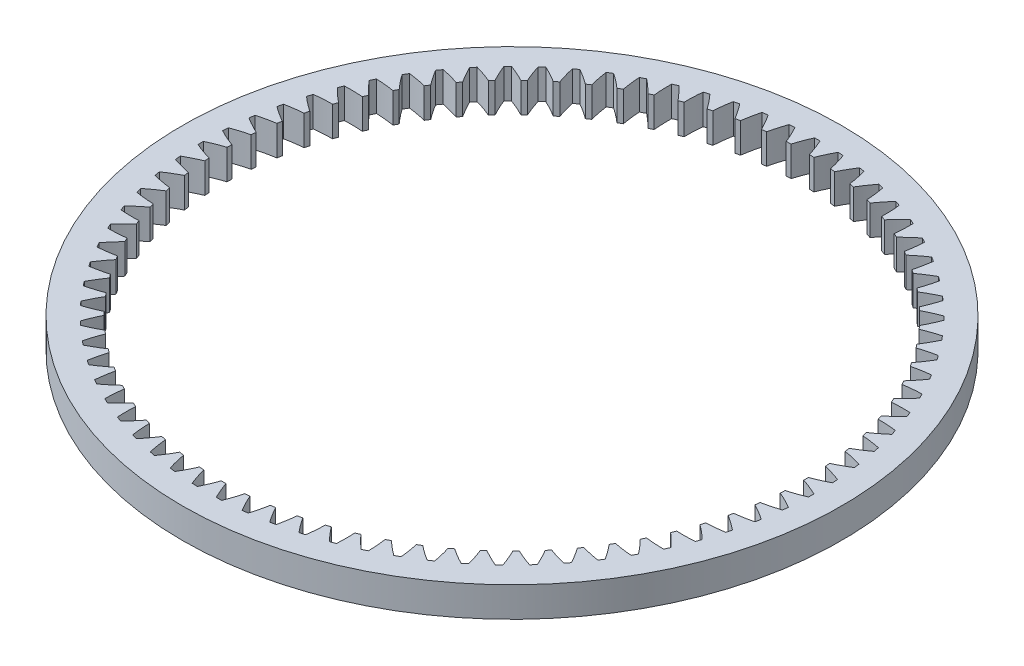
SolidWorks part; units mm, degrees
ref_plane "Front Plane" through (0, 0, 0) normal (0, 0, 1) x (1, 0, 0)
ref_plane "Top Plane" through (0, 0, 0) normal (0, 1, 0) x (1, 0, 0)
ref_plane "Right Plane" through (0, 0, 0) normal (1, 0, 0) x (0, 0, -1)
sketch "Sketch1" plane through (0, 0, 0) normal (0, 1, 0) x (1, 0, 0)
  line L0 (0, 52.5562) -> (0, -52.5562) construction
  circle A0 centre (0, 0) radius 29.5 construction
  circle A1 centre (0, 0) radius 30.56 construction
  arc A2 (-21.0185, 24.6048) -> (-21.4508, 24.2287) centre (0, 0) ccw
  circle A3 centre (0, 0) radius 34.925
  arc A4 (-0.2865, 32.3587) -> (-0.9677, 30.5447) centre (14.0429, 25.9432) ccw
  arc A5 (0.9677, 30.5447) -> (0.2865, 32.3587) centre (-14.0429, 25.9432) ccw
  arc A6 (-5.7937, 30.0058) -> (-6.2788, 29.908) centre (0, 0) ccw
  arc A7 (2.2853, 32.2792) -> (1.4622, 30.525) centre (16.0597, 24.7455) ccw
  arc A8 (3.3914, 30.3712) -> (2.8565, 32.2337) centre (-11.9373, 26.9769) ccw
  arc A9 (4.8427, 31.9956) -> (3.8828, 30.3123) centre (17.9749, 23.3913) ccw
  arc A10 (5.7937, 30.0058) -> (5.4084, 31.9048) centre (-9.7562, 27.84) ccw
  arc A11 (7.3694, 31.5097) -> (6.2788, 29.908) centre (19.7765, 21.8892) ccw
  arc A12 (8.1593, 29.4506) -> (7.9262, 31.3743) centre (-7.5135, 28.5271) ccw
  arc A13 (9.8496, 30.8246) -> (8.6352, 29.3146) centre (21.4531, 20.2488) ccw
  arc A14 (10.4734, 28.7093) -> (10.3938, 30.6454) centre (-5.2233, 29.0339) ccw
  arc A15 (12.2675, 29.9446) -> (10.9369, 28.5359) centre (22.9941, 18.4803) ccw
  arc A16 (12.7212, 27.7864) -> (12.7957, 29.7227) centre (-2.9, 29.3571) ccw
  arc A17 (14.6078, 28.8753) -> (13.1695, 27.5768) centre (24.3897, 16.595) ccw
  arc A18 (14.8887, 26.6879) -> (15.1168, 28.6121) centre (-0.5584, 29.4947) ccw
  arc A19 (16.8558, 27.6234) -> (15.3189, 26.4433) centre (25.631, 14.6048) ccw
  arc A20 (16.9619, 25.4206) -> (17.3422, 27.3206) centre (1.7867, 29.4458) ccw
  arc A21 (18.9972, 26.1969) -> (17.3714, 25.1426) centre (26.7104, 12.5222) ccw
  arc A22 (18.928, 23.9926) -> (19.458, 25.8564) centre (4.1206, 29.2108) ccw
  arc A23 (21.0185, 24.6048) -> (19.314, 23.6829) centre (27.6208, 10.3605) ccw
  arc A24 (20.7744, 22.4129) -> (21.4508, 24.2287) centre (6.4283, 28.7911) ccw
  arc A25 (22.9069, 22.8571) -> (21.1346, 22.0736) centre (28.3567, 8.1333) ccw
  arc A26 (22.4894, 20.6915) -> (23.308, 22.4479) centre (8.6955, 28.1893) ccw
  arc A27 (24.6504, 20.9649) -> (22.8215, 20.3247) centre (28.9132, 5.8546) ccw
  arc A28 (24.0623, 18.8393) -> (25.0178, 20.5251) centre (10.9076, 27.4094) ccw
  arc A29 (26.2382, 18.9401) -> (24.3642, 18.4472) centre (29.287, 3.539) ccw
  arc A30 (25.483, 16.868) -> (26.5694, 18.4725) centre (13.0508, 26.4561) ccw
  arc A31 (27.66, 16.7956) -> (25.7528, 16.4532) centre (29.4755, 1.2009) ccw
  arc A32 (26.7426, 14.7901) -> (27.9531, 16.3032) centre (15.1115, 25.3356) ccw
  arc A33 (28.907, 14.5449) -> (26.9786, 14.3551) centre (29.4778, -1.1447) ccw
  arc A34 (27.8331, 12.6186) -> (29.16, 14.0308) centre (17.0767, 24.0549) ccw
  arc A35 (29.9712, 12.2023) -> (28.0338, 12.1663) centre (29.2937, -3.4831) ccw
  arc A36 (28.7477, 10.3674) -> (30.1826, 11.6697) centre (18.9338, 22.6221) ccw
  arc A37 (30.846, 9.7825) -> (28.9118, 9.9005) centre (28.9243, -5.7995) ccw
  arc A38 (29.4805, 8.0506) -> (31.0143, 9.2348) centre (20.6713, 21.0463) ccw
  arc A39 (31.5257, 7.3008) -> (29.607, 7.5722) centre (28.3721, -8.0792) ccw
  arc A40 (30.027, 5.6829) -> (31.65, 6.7415) centre (22.2781, 19.3374) ccw
  arc A41 (32.0061, 4.773) -> (30.115, 5.1959) centre (27.6405, -10.3078) ccw
  arc A42 (30.3835, 3.2793) -> (32.0856, 4.2056) centre (23.744, 17.5063) ccw
  arc A43 (32.2841, 2.2151) -> (30.4327, 2.7869) centre (26.7342, -12.4713) ccw
  arc A44 (30.548, 0.855) -> (32.3183, 1.6431) centre (25.0599, 15.5645) ccw
  arc A45 (32.358, -0.3569) -> (30.5579, 0.3602) centre (25.6588, -14.5559) ccw
  arc A46 (30.5194, -1.5748) -> (32.3466, -0.9298) centre (26.2172, 13.5243) ccw
  arc A47 (32.2274, -2.9266) -> (30.4899, -2.0688) centre (24.4213, -16.5485) ccw
  arc A48 (30.2978, -3.9946) -> (32.1705, -3.4968) centre (27.2089, 11.3986) ccw
  arc A49 (31.893, -5.4779) -> (30.2291, -4.4847) centre (23.0293, -18.4364) ccw
  arc A50 (29.8847, -6.3891) -> (31.791, -6.0417) centre (28.0285, 9.2008) ccw
  arc A51 (31.357, -7.9944) -> (29.7773, -6.8722) centre (21.4917, -20.2078) ccw
  arc A52 (29.2826, -8.7433) -> (31.2105, -8.5484) centre (28.6709, 6.9448) ccw
  arc A53 (30.6227, -10.4605) -> (29.1372, -9.2163) centre (19.8182, -21.8515) ccw
  arc A54 (28.4954, -11.0421) -> (30.4326, -11.0011) centre (29.132, 4.645) ccw
  arc A55 (29.6948, -12.8604) -> (28.3128, -11.5021) centre (18.0195, -23.357) ccw
  arc A56 (27.528, -13.2712) -> (29.4624, -13.3842) centre (29.409, 2.3157) ccw
  arc A57 (28.5791, -15.179) -> (27.3095, -13.7152) centre (16.1068, -24.7148) ccw
  arc A58 (26.3866, -15.4163) -> (28.3059, -15.6827) centre (29.5, -0.0281) ccw
  arc A59 (27.2828, -17.4016) -> (26.1335, -15.8416) centre (14.0923, -25.9163) ccw
  arc A60 (25.0783, -17.464) -> (26.9704, -17.882) centre (29.4045, -2.3718) ccw
  arc A61 (25.814, -19.5143) -> (24.7922, -17.8678) centre (11.9887, -26.9541) ccw
  arc A62 (23.6115, -19.4013) -> (25.4644, -19.9683) centre (29.1231, -4.7005) ccw
  arc A63 (24.182, -21.5035) -> (23.2943, -19.7811) centre (9.8093, -27.8214) ccw
  arc A64 (21.9954, -21.2159) -> (23.7975, -21.9283) centre (28.6576, -6.9995) ccw
  arc A65 (22.3971, -23.3568) -> (21.649, -21.5693) centre (7.5679, -28.5128) ccw
  arc A66 (20.2403, -22.8964) -> (21.98, -23.7497) centre (28.0109, -9.2542) ccw
  arc A67 (20.4706, -25.0624) -> (19.8669, -23.2211) centre (5.2786, -29.0239) ccw
  arc A68 (18.3572, -24.4321) -> (20.0236, -25.4209) centre (27.1871, -11.4504) ccw
  arc A69 (18.4147, -26.6096) -> (17.9592, -24.7261) centre (2.956, -29.3515) ccw
  arc A70 (16.358, -25.8133) -> (17.9406, -26.9315) centre (26.1914, -13.5743) ccw
  arc A71 (16.2423, -27.9885) -> (15.9379, -26.0748) centre (0.6146, -29.4936) ccw
  arc A72 (14.2555, -27.0314) -> (15.7442, -28.2717) centre (25.0301, -15.6123) ccw
  arc A73 (13.9673, -29.1905) -> (13.8159, -27.2587) centre (-1.7306, -29.4492) ccw
  arc A74 (12.0628, -28.0785) -> (13.4483, -29.4332) centre (23.7106, -17.5515) ccw
  arc A75 (11.604, -30.2079) -> (11.6065, -28.2702) centre (-4.0648, -29.2186) ccw
  arc A76 (9.7938, -28.9482) -> (11.0673, -30.4086) centre (22.2412, -19.3799) ccw
  arc A77 (9.1673, -31.0344) -> (9.3237, -29.103) centre (-6.3734, -28.8033) ccw
  arc A78 (7.4629, -29.6348) -> (8.6163, -31.1918) centre (20.6311, -21.0857) ccw
  arc A79 (6.6726, -31.6646) -> (6.982, -29.7517) centre (-8.6417, -28.2059) ccw
  arc A80 (5.0848, -30.134) -> (6.1109, -31.7778) centre (18.8907, -22.6582) ccw
  arc A81 (4.1357, -32.0946) -> (4.5962, -30.2124) centre (-10.8553, -27.4301) ccw
  arc A82 (2.6746, -30.4427) -> (3.5668, -32.1628) centre (17.0308, -24.0874) ccw
  arc A83 (1.5727, -32.3218) -> (2.1813, -30.4821) centre (-13.0003, -26.481) ccw
  arc A84 (0.2474, -30.559) -> (1.0002, -32.3445) centre (15.0632, -25.3644) ccw
  arc A85 (-1.0002, -32.3445) -> (-0.2474, -30.559) centre (-15.0632, -25.3644) ccw
  arc A86 (-2.1813, -30.4821) -> (-1.5727, -32.3218) centre (13.0003, -26.481) ccw
  arc A87 (-3.5668, -32.1628) -> (-2.6746, -30.4427) centre (-17.0308, -24.0874) ccw
  arc A88 (-4.5962, -30.2124) -> (-4.1357, -32.0946) centre (10.8553, -27.4301) ccw
  arc A89 (-6.1109, -31.7778) -> (-5.0848, -30.134) centre (-18.8907, -22.6582) ccw
  arc A90 (-6.982, -29.7517) -> (-6.6726, -31.6646) centre (8.6417, -28.2059) ccw
  arc A91 (-8.6163, -31.1918) -> (-7.4629, -29.6348) centre (-20.6311, -21.0857) ccw
  arc A92 (-9.3237, -29.103) -> (-9.1673, -31.0344) centre (6.3734, -28.8033) ccw
  arc A93 (-11.0673, -30.4086) -> (-9.7938, -28.9482) centre (-22.2412, -19.3799) ccw
  arc A94 (-11.6065, -28.2702) -> (-11.604, -30.2079) centre (4.0648, -29.2186) ccw
  arc A95 (-13.4483, -29.4332) -> (-12.0628, -28.0785) centre (-23.7106, -17.5515) ccw
  arc A96 (-13.8159, -27.2587) -> (-13.9673, -29.1905) centre (1.7306, -29.4492) ccw
  arc A97 (-15.7442, -28.2717) -> (-14.2555, -27.0314) centre (-25.0301, -15.6123) ccw
  arc A98 (-15.9379, -26.0748) -> (-16.2423, -27.9885) centre (-0.6146, -29.4936) ccw
  arc A99 (-17.9406, -26.9315) -> (-16.358, -25.8133) centre (-26.1914, -13.5743) ccw
  arc A100 (-17.9592, -24.7261) -> (-18.4147, -26.6096) centre (-2.956, -29.3515) ccw
  arc A101 (-20.0236, -25.4209) -> (-18.3572, -24.4321) centre (-27.1871, -11.4504) ccw
  arc A102 (-19.8669, -23.2211) -> (-20.4706, -25.0624) centre (-5.2786, -29.0239) ccw
  arc A103 (-21.98, -23.7497) -> (-20.2403, -22.8964) centre (-28.0109, -9.2542) ccw
  arc A104 (-21.649, -21.5693) -> (-22.3971, -23.3568) centre (-7.5679, -28.5128) ccw
  arc A105 (-23.7975, -21.9283) -> (-21.9954, -21.2159) centre (-28.6576, -6.9995) ccw
  arc A106 (-23.2943, -19.7811) -> (-24.182, -21.5035) centre (-9.8093, -27.8214) ccw
  arc A107 (-25.4644, -19.9683) -> (-23.6115, -19.4013) centre (-29.1231, -4.7005) ccw
  arc A108 (-24.7922, -17.8678) -> (-25.814, -19.5143) centre (-11.9887, -26.9541) ccw
  arc A109 (-26.9704, -17.882) -> (-25.0783, -17.464) centre (-29.4045, -2.3718) ccw
  arc A110 (-26.1335, -15.8416) -> (-27.2828, -17.4016) centre (-14.0923, -25.9163) ccw
  arc A111 (-28.3059, -15.6827) -> (-26.3866, -15.4163) centre (-29.5, -0.0281) ccw
  arc A112 (-27.3095, -13.7152) -> (-28.5791, -15.179) centre (-16.1068, -24.7148) ccw
  arc A113 (-29.4624, -13.3842) -> (-27.528, -13.2712) centre (-29.409, 2.3157) ccw
  arc A114 (-28.3128, -11.5021) -> (-29.6948, -12.8604) centre (-18.0195, -23.357) ccw
  arc A115 (-30.4326, -11.0011) -> (-28.4954, -11.0421) centre (-29.132, 4.645) ccw
  arc A116 (-29.1372, -9.2163) -> (-30.6227, -10.4605) centre (-19.8182, -21.8515) ccw
  arc A117 (-31.2105, -8.5484) -> (-29.2826, -8.7433) centre (-28.6709, 6.9448) ccw
  arc A118 (-29.7773, -6.8722) -> (-31.357, -7.9944) centre (-21.4917, -20.2078) ccw
  arc A119 (-31.791, -6.0417) -> (-29.8847, -6.3891) centre (-28.0285, 9.2008) ccw
  arc A120 (-30.2291, -4.4847) -> (-31.893, -5.4779) centre (-23.0293, -18.4364) ccw
  arc A121 (-32.1705, -3.4968) -> (-30.2978, -3.9946) centre (-27.2089, 11.3986) ccw
  arc A122 (-30.4899, -2.0688) -> (-32.2274, -2.9266) centre (-24.4213, -16.5485) ccw
  arc A123 (-32.3466, -0.9298) -> (-30.5194, -1.5748) centre (-26.2172, 13.5243) ccw
  arc A124 (-30.5579, 0.3602) -> (-32.358, -0.3569) centre (-25.6588, -14.5559) ccw
  arc A125 (-32.3183, 1.6431) -> (-30.548, 0.855) centre (-25.0599, 15.5645) ccw
  arc A126 (-30.4327, 2.7869) -> (-32.2841, 2.2151) centre (-26.7342, -12.4713) ccw
  arc A127 (-32.0856, 4.2056) -> (-30.3835, 3.2793) centre (-23.744, 17.5063) ccw
  arc A128 (-30.115, 5.1959) -> (-32.0061, 4.773) centre (-27.6405, -10.3078) ccw
  arc A129 (-31.65, 6.7415) -> (-30.027, 5.6829) centre (-22.2781, 19.3374) ccw
  arc A130 (-29.607, 7.5722) -> (-31.5257, 7.3008) centre (-28.3721, -8.0792) ccw
  arc A131 (-31.0143, 9.2348) -> (-29.4805, 8.0506) centre (-20.6713, 21.0463) ccw
  arc A132 (-28.9118, 9.9005) -> (-30.846, 9.7825) centre (-28.9243, -5.7995) ccw
  arc A133 (-30.1826, 11.6697) -> (-28.7477, 10.3674) centre (-18.9338, 22.6221) ccw
  arc A134 (-28.0338, 12.1663) -> (-29.9712, 12.2023) centre (-29.2937, -3.4831) ccw
  arc A135 (-29.16, 14.0308) -> (-27.8331, 12.6186) centre (-17.0767, 24.0549) ccw
  arc A136 (-26.9786, 14.3551) -> (-28.907, 14.5449) centre (-29.4778, -1.1447) ccw
  arc A137 (-27.9531, 16.3032) -> (-26.7426, 14.7901) centre (-15.1115, 25.3356) ccw
  arc A138 (-25.7528, 16.4532) -> (-27.66, 16.7956) centre (-29.4755, 1.2009) ccw
  arc A139 (-26.5694, 18.4725) -> (-25.483, 16.868) centre (-13.0508, 26.4561) ccw
  arc A140 (-24.3642, 18.4472) -> (-26.2382, 18.9401) centre (-29.287, 3.539) ccw
  arc A141 (-25.0178, 20.5251) -> (-24.0623, 18.8393) centre (-10.9076, 27.4094) ccw
  arc A142 (-22.8215, 20.3247) -> (-24.6504, 20.9649) centre (-28.9132, 5.8546) ccw
  arc A143 (-23.308, 22.4479) -> (-22.4894, 20.6915) centre (-8.6955, 28.1893) ccw
  arc A144 (-21.1346, 22.0736) -> (-22.9069, 22.8571) centre (-28.3567, 8.1333) ccw
  arc A145 (-21.4508, 24.2287) -> (-20.7744, 22.4129) centre (-6.4283, 28.7911) ccw
  arc A146 (-19.314, 23.6829) -> (-21.0185, 24.6048) centre (-27.6208, 10.3605) ccw
  arc A147 (-19.458, 25.8564) -> (-18.928, 23.9926) centre (-4.1206, 29.2108) ccw
  arc A148 (-17.3714, 25.1426) -> (-18.9972, 26.1969) centre (-26.7104, 12.5222) ccw
  arc A149 (-17.3422, 27.3206) -> (-16.9619, 25.4206) centre (-1.7867, 29.4458) ccw
  arc A150 (-15.3189, 26.4433) -> (-16.8558, 27.6234) centre (-25.631, 14.6048) ccw
  arc A151 (-15.1168, 28.6121) -> (-14.8887, 26.6879) centre (0.5584, 29.4947) ccw
  arc A152 (-13.1695, 27.5768) -> (-14.6078, 28.8753) centre (-24.3897, 16.595) ccw
  arc A153 (-12.7957, 29.7227) -> (-12.7212, 27.7864) centre (2.9, 29.3571) ccw
  arc A154 (-10.9369, 28.5359) -> (-12.2675, 29.9446) centre (-22.9941, 18.4803) ccw
  arc A155 (-10.3938, 30.6454) -> (-10.4734, 28.7093) centre (5.2233, 29.0339) ccw
  arc A156 (-8.6352, 29.3146) -> (-9.8496, 30.8246) centre (-21.4531, 20.2488) ccw
  arc A157 (-7.9262, 31.3743) -> (-8.1593, 29.4506) centre (7.5135, 28.5271) ccw
  arc A158 (-6.2788, 29.908) -> (-7.3694, 31.5097) centre (-19.7765, 21.8892) ccw
  arc A159 (-5.4084, 31.9048) -> (-5.7937, 30.0058) centre (9.7562, 27.84) ccw
  arc A160 (-3.8828, 30.3123) -> (-4.8427, 31.9956) centre (-17.9749, 23.3913) ccw
  arc A161 (-2.8565, 32.2337) -> (-3.3914, 30.3712) centre (11.9373, 26.9769) ccw
  arc A162 (-1.4622, 30.525) -> (-2.2853, 32.2792) centre (-16.0597, 24.7455) ccw
  arc A163 (-3.3914, 30.3712) -> (-3.8828, 30.3123) centre (0, 0) ccw
  arc A164 (-0.9677, 30.5447) -> (-1.4622, 30.525) centre (0, 0) ccw
  arc A165 (1.4622, 30.525) -> (0.9677, 30.5447) centre (0, 0) ccw
  arc A166 (3.8828, 30.3123) -> (3.3914, 30.3712) centre (0, 0) ccw
  arc A167 (6.2788, 29.908) -> (5.7937, 30.0058) centre (0, 0) ccw
  arc A168 (8.6352, 29.3146) -> (8.1593, 29.4506) centre (0, 0) ccw
  arc A169 (10.9369, 28.5359) -> (10.4734, 28.7093) centre (0, 0) ccw
  arc A170 (13.1695, 27.5768) -> (12.7212, 27.7864) centre (0, 0) ccw
  arc A171 (-8.1593, 29.4506) -> (-8.6352, 29.3146) centre (0, 0) ccw
  arc A172 (-10.4734, 28.7093) -> (-10.9369, 28.5359) centre (0, 0) ccw
  arc A173 (-12.7212, 27.7864) -> (-13.1695, 27.5768) centre (0, 0) ccw
  arc A174 (-14.8887, 26.6879) -> (-15.3189, 26.4433) centre (0, 0) ccw
  arc A175 (-16.9619, 25.4206) -> (-17.3714, 25.1426) centre (0, 0) ccw
  arc A176 (-18.928, 23.9926) -> (-19.314, 23.6829) centre (0, 0) ccw
  arc A177 (-20.7744, 22.4129) -> (-21.1346, 22.0736) centre (0, 0) ccw
  arc A178 (-18.9972, 26.1969) -> (-19.458, 25.8564) centre (0, 0) ccw
  arc A179 (-16.8558, 27.6234) -> (-17.3422, 27.3206) centre (0, 0) ccw
  arc A180 (-14.6078, 28.8753) -> (-15.1168, 28.6121) centre (0, 0) ccw
  arc A181 (-12.2675, 29.9446) -> (-12.7957, 29.7227) centre (0, 0) ccw
  arc A182 (-9.8496, 30.8246) -> (-10.3938, 30.6454) centre (0, 0) ccw
  arc A183 (-7.3694, 31.5097) -> (-7.9262, 31.3743) centre (0, 0) ccw
  arc A184 (-4.8427, 31.9956) -> (-5.4084, 31.9048) centre (0, 0) ccw
  arc A185 (-2.2853, 32.2792) -> (-2.8565, 32.2337) centre (0, 0) ccw
  arc A186 (0.2865, 32.3587) -> (-0.2865, 32.3587) centre (0, 0) ccw
  arc A187 (2.8565, 32.2337) -> (2.2853, 32.2792) centre (0, 0) ccw
  arc A188 (5.4084, 31.9048) -> (4.8427, 31.9956) centre (0, 0) ccw
  arc A189 (7.9262, 31.3743) -> (7.3694, 31.5097) centre (0, 0) ccw
  arc A190 (10.3938, 30.6454) -> (9.8496, 30.8246) centre (0, 0) ccw
  arc A191 (12.7957, 29.7227) -> (12.2675, 29.9446) centre (0, 0) ccw
  arc A192 (-22.9069, 22.8571) -> (-23.308, 22.4479) centre (0, 0) ccw
  arc A193 (-24.6504, 20.9649) -> (-25.0178, 20.5251) centre (0, 0) ccw
  arc A194 (-26.2382, 18.9401) -> (-26.5694, 18.4725) centre (0, 0) ccw
  arc A195 (-27.66, 16.7956) -> (-27.9531, 16.3032) centre (0, 0) ccw
  arc A196 (-28.907, 14.5449) -> (-29.16, 14.0308) centre (0, 0) ccw
  arc A197 (-29.9712, 12.2023) -> (-30.1826, 11.6697) centre (0, 0) ccw
  arc A198 (-30.846, 9.7825) -> (-31.0143, 9.2348) centre (0, 0) ccw
  arc A199 (-31.5257, 7.3008) -> (-31.65, 6.7415) centre (0, 0) ccw
  arc A200 (-32.0061, 4.773) -> (-32.0856, 4.2056) centre (0, 0) ccw
  arc A201 (-32.2841, 2.2151) -> (-32.3183, 1.6431) centre (0, 0) ccw
  arc A202 (-32.358, -0.3569) -> (-32.3466, -0.9298) centre (0, 0) ccw
  arc A203 (-32.2274, -2.9266) -> (-32.1705, -3.4968) centre (0, 0) ccw
  arc A204 (-31.893, -5.4779) -> (-31.791, -6.0417) centre (0, 0) ccw
  arc A205 (-31.357, -7.9944) -> (-31.2105, -8.5484) centre (0, 0) ccw
  arc A206 (-30.6227, -10.4605) -> (-30.4326, -11.0011) centre (0, 0) ccw
  arc A207 (-29.6948, -12.8604) -> (-29.4624, -13.3842) centre (0, 0) ccw
  arc A208 (-28.5791, -15.179) -> (-28.3059, -15.6827) centre (0, 0) ccw
  arc A209 (-27.528, -13.2712) -> (-27.3095, -13.7152) centre (0, 0) ccw
  arc A210 (-26.3866, -15.4163) -> (-26.1335, -15.8416) centre (0, 0) ccw
  arc A211 (-28.4954, -11.0421) -> (-28.3128, -11.5021) centre (0, 0) ccw
  arc A212 (-29.2826, -8.7433) -> (-29.1372, -9.2163) centre (0, 0) ccw
  arc A213 (-29.8847, -6.3891) -> (-29.7773, -6.8722) centre (0, 0) ccw
  arc A214 (-30.2978, -3.9946) -> (-30.2291, -4.4847) centre (0, 0) ccw
  arc A215 (-30.5194, -1.5748) -> (-30.4899, -2.0688) centre (0, 0) ccw
  arc A216 (-30.548, 0.855) -> (-30.5579, 0.3602) centre (0, 0) ccw
  arc A217 (-30.3835, 3.2793) -> (-30.4327, 2.7869) centre (0, 0) ccw
  arc A218 (-30.027, 5.6829) -> (-30.115, 5.1959) centre (0, 0) ccw
  arc A219 (-29.4805, 8.0506) -> (-29.607, 7.5722) centre (0, 0) ccw
  arc A220 (-28.7477, 10.3674) -> (-28.9118, 9.9005) centre (0, 0) ccw
  arc A221 (-27.8331, 12.6186) -> (-28.0338, 12.1663) centre (0, 0) ccw
  arc A222 (-26.7426, 14.7901) -> (-26.9786, 14.3551) centre (0, 0) ccw
  arc A223 (-25.483, 16.868) -> (-25.7528, 16.4532) centre (0, 0) ccw
  arc A224 (-24.0623, 18.8393) -> (-24.3642, 18.4472) centre (0, 0) ccw
  arc A225 (-22.4894, 20.6915) -> (-22.8215, 20.3247) centre (0, 0) ccw
  arc A226 (15.1168, 28.6121) -> (14.6078, 28.8753) centre (0, 0) ccw
  arc A227 (17.3422, 27.3206) -> (16.8558, 27.6234) centre (0, 0) ccw
  arc A228 (19.458, 25.8564) -> (18.9972, 26.1969) centre (0, 0) ccw
  arc A229 (21.4508, 24.2287) -> (21.0185, 24.6048) centre (0, 0) ccw
  arc A230 (23.308, 22.4479) -> (22.9069, 22.8571) centre (0, 0) ccw
  arc A231 (25.0178, 20.5251) -> (24.6504, 20.9649) centre (0, 0) ccw
  arc A232 (26.5694, 18.4725) -> (26.2382, 18.9401) centre (0, 0) ccw
  arc A233 (27.9531, 16.3032) -> (27.66, 16.7956) centre (0, 0) ccw
  arc A234 (29.16, 14.0308) -> (28.907, 14.5449) centre (0, 0) ccw
  arc A235 (30.1826, 11.6697) -> (29.9712, 12.2023) centre (0, 0) ccw
  arc A236 (31.0143, 9.2348) -> (30.846, 9.7825) centre (0, 0) ccw
  arc A237 (31.65, 6.7415) -> (31.5257, 7.3008) centre (0, 0) ccw
  arc A238 (32.0856, 4.2056) -> (32.0061, 4.773) centre (0, 0) ccw
  arc A239 (32.3183, 1.6431) -> (32.2841, 2.2151) centre (0, 0) ccw
  arc A240 (32.3466, -0.9298) -> (32.358, -0.3569) centre (0, 0) ccw
  arc A241 (32.1705, -3.4968) -> (32.2274, -2.9266) centre (0, 0) ccw
  arc A242 (31.791, -6.0417) -> (31.893, -5.4779) centre (0, 0) ccw
  arc A243 (31.2105, -8.5484) -> (31.357, -7.9944) centre (0, 0) ccw
  arc A244 (30.4326, -11.0011) -> (30.6227, -10.4605) centre (0, 0) ccw
  arc A245 (29.4624, -13.3842) -> (29.6948, -12.8604) centre (0, 0) ccw
  arc A246 (28.3059, -15.6827) -> (28.5791, -15.179) centre (0, 0) ccw
  arc A247 (26.1335, -15.8416) -> (26.3866, -15.4163) centre (0, 0) ccw
  arc A248 (27.3095, -13.7152) -> (27.528, -13.2712) centre (0, 0) ccw
  arc A249 (28.3128, -11.5021) -> (28.4954, -11.0421) centre (0, 0) ccw
  arc A250 (29.1372, -9.2163) -> (29.2826, -8.7433) centre (0, 0) ccw
  arc A251 (29.7773, -6.8722) -> (29.8847, -6.3891) centre (0, 0) ccw
  arc A252 (30.2291, -4.4847) -> (30.2978, -3.9946) centre (0, 0) ccw
  arc A253 (30.4899, -2.0688) -> (30.5194, -1.5748) centre (0, 0) ccw
  arc A254 (30.5579, 0.3602) -> (30.548, 0.855) centre (0, 0) ccw
  arc A255 (30.4327, 2.7869) -> (30.3835, 3.2793) centre (0, 0) ccw
  arc A256 (30.115, 5.1959) -> (30.027, 5.6829) centre (0, 0) ccw
  arc A257 (29.607, 7.5722) -> (29.4805, 8.0506) centre (0, 0) ccw
  arc A258 (28.9118, 9.9005) -> (28.7477, 10.3674) centre (0, 0) ccw
  arc A259 (28.0338, 12.1663) -> (27.8331, 12.6186) centre (0, 0) ccw
  arc A260 (26.9786, 14.3551) -> (26.7426, 14.7901) centre (0, 0) ccw
  arc A261 (25.7528, 16.4532) -> (25.483, 16.868) centre (0, 0) ccw
  arc A262 (24.3642, 18.4472) -> (24.0623, 18.8393) centre (0, 0) ccw
  arc A263 (22.8215, 20.3247) -> (22.4894, 20.6915) centre (0, 0) ccw
  arc A264 (21.1346, 22.0736) -> (20.7744, 22.4129) centre (0, 0) ccw
  arc A265 (19.314, 23.6829) -> (18.928, 23.9926) centre (0, 0) ccw
  arc A266 (17.3714, 25.1426) -> (16.9619, 25.4206) centre (0, 0) ccw
  arc A267 (15.3189, 26.4433) -> (14.8887, 26.6879) centre (0, 0) ccw
  arc A268 (-27.2828, -17.4016) -> (-26.9704, -17.882) centre (0, 0) ccw
  arc A269 (-25.814, -19.5143) -> (-25.4644, -19.9683) centre (0, 0) ccw
  arc A270 (-24.182, -21.5035) -> (-23.7975, -21.9283) centre (0, 0) ccw
  arc A271 (-22.3971, -23.3568) -> (-21.98, -23.7497) centre (0, 0) ccw
  arc A272 (-20.4706, -25.0624) -> (-20.0236, -25.4209) centre (0, 0) ccw
  arc A273 (-18.4147, -26.6096) -> (-17.9406, -26.9315) centre (0, 0) ccw
  arc A274 (-16.2423, -27.9885) -> (-15.7442, -28.2717) centre (0, 0) ccw
  arc A275 (-13.9673, -29.1905) -> (-13.4483, -29.4332) centre (0, 0) ccw
  arc A276 (-11.604, -30.2079) -> (-11.0673, -30.4086) centre (0, 0) ccw
  arc A277 (-9.1673, -31.0344) -> (-8.6163, -31.1918) centre (0, 0) ccw
  arc A278 (-6.6726, -31.6646) -> (-6.1109, -31.7778) centre (0, 0) ccw
  arc A279 (-4.1357, -32.0946) -> (-3.5668, -32.1628) centre (0, 0) ccw
  arc A280 (-1.5727, -32.3218) -> (-1.0002, -32.3445) centre (0, 0) ccw
  arc A281 (1.0002, -32.3445) -> (1.5727, -32.3218) centre (0, 0) ccw
  arc A282 (3.5668, -32.1628) -> (4.1357, -32.0946) centre (0, 0) ccw
  arc A283 (6.1109, -31.7778) -> (6.6726, -31.6646) centre (0, 0) ccw
  arc A284 (8.6163, -31.1918) -> (9.1673, -31.0344) centre (0, 0) ccw
  arc A285 (11.0673, -30.4086) -> (11.604, -30.2079) centre (0, 0) ccw
  arc A286 (13.4483, -29.4332) -> (13.9673, -29.1905) centre (0, 0) ccw
  arc A287 (15.7442, -28.2717) -> (16.2423, -27.9885) centre (0, 0) ccw
  arc A288 (17.9406, -26.9315) -> (18.4147, -26.6096) centre (0, 0) ccw
  arc A289 (20.0236, -25.4209) -> (20.4706, -25.0624) centre (0, 0) ccw
  arc A290 (21.98, -23.7497) -> (22.3971, -23.3568) centre (0, 0) ccw
  arc A291 (23.7975, -21.9283) -> (24.182, -21.5035) centre (0, 0) ccw
  arc A292 (25.4644, -19.9683) -> (25.814, -19.5143) centre (0, 0) ccw
  arc A293 (26.9704, -17.882) -> (27.2828, -17.4016) centre (0, 0) ccw
  arc A294 (24.7922, -17.8678) -> (25.0783, -17.464) centre (0, 0) ccw
  arc A295 (23.2943, -19.7811) -> (23.6115, -19.4013) centre (0, 0) ccw
  arc A296 (21.649, -21.5693) -> (21.9954, -21.2159) centre (0, 0) ccw
  arc A297 (19.8669, -23.2211) -> (20.2403, -22.8964) centre (0, 0) ccw
  arc A298 (17.9592, -24.7261) -> (18.3572, -24.4321) centre (0, 0) ccw
  arc A299 (15.9379, -26.0748) -> (16.358, -25.8133) centre (0, 0) ccw
  arc A300 (13.8159, -27.2587) -> (14.2555, -27.0314) centre (0, 0) ccw
  arc A301 (11.6065, -28.2702) -> (12.0628, -28.0785) centre (0, 0) ccw
  arc A302 (9.3237, -29.103) -> (9.7938, -28.9482) centre (0, 0) ccw
  arc A303 (6.982, -29.7517) -> (7.4629, -29.6348) centre (0, 0) ccw
  arc A304 (4.5962, -30.2124) -> (5.0848, -30.134) centre (0, 0) ccw
  arc A305 (2.1813, -30.4821) -> (2.6746, -30.4427) centre (0, 0) ccw
  arc A306 (-0.2474, -30.559) -> (0.2474, -30.559) centre (0, 0) ccw
  arc A307 (-2.6746, -30.4427) -> (-2.1813, -30.4821) centre (0, 0) ccw
  arc A308 (-5.0848, -30.134) -> (-4.5962, -30.2124) centre (0, 0) ccw
  arc A309 (-7.4629, -29.6348) -> (-6.982, -29.7517) centre (0, 0) ccw
  arc A310 (-9.7938, -28.9482) -> (-9.3237, -29.103) centre (0, 0) ccw
  arc A311 (-12.0628, -28.0785) -> (-11.6065, -28.2702) centre (0, 0) ccw
  arc A312 (-14.2555, -27.0314) -> (-13.8159, -27.2587) centre (0, 0) ccw
  arc A313 (-16.358, -25.8133) -> (-15.9379, -26.0748) centre (0, 0) ccw
  arc A314 (-18.3572, -24.4321) -> (-17.9592, -24.7261) centre (0, 0) ccw
  arc A315 (-20.2403, -22.8964) -> (-19.8669, -23.2211) centre (0, 0) ccw
  arc A316 (-21.9954, -21.2159) -> (-21.649, -21.5693) centre (0, 0) ccw
  arc A317 (-23.6115, -19.4013) -> (-23.2943, -19.7811) centre (0, 0) ccw
  arc A318 (-25.0783, -17.464) -> (-24.7922, -17.8678) centre (0, 0) ccw
  point P10 (-0.2865, 32.3587)
  point P11 (0.2865, 32.3587)
  point P15 (0, 0)
  point P488 (0, 0)
  dimension "D1" = 29.5
  dimension "D2" = 30.56
  dimension "D3" = 32.36
  dimension "D4" = 69.85
  dimension "D5" = 15.7
  dimension "D8" = 79
  dimension "D6" = 0.573
  dimension "D7" = 0.2865
extrude "Boss-Extrude1" add sketch "Sketch1" along normal blind 3.175 contours A3 A318 A109 A268 A110 A210 A111 A208 A112 A209 A113 A207 A114 A211 A115 A206 A116 A212 A117 A205 A118 A213 A119 A204 A120 A214 A121 A203 A122 A215 A123 A202 A124 A216 A125 A201 A126 A217 A127 A200 A128 A218 A129 A199 A130 A219 A131 A198 A132 A220
